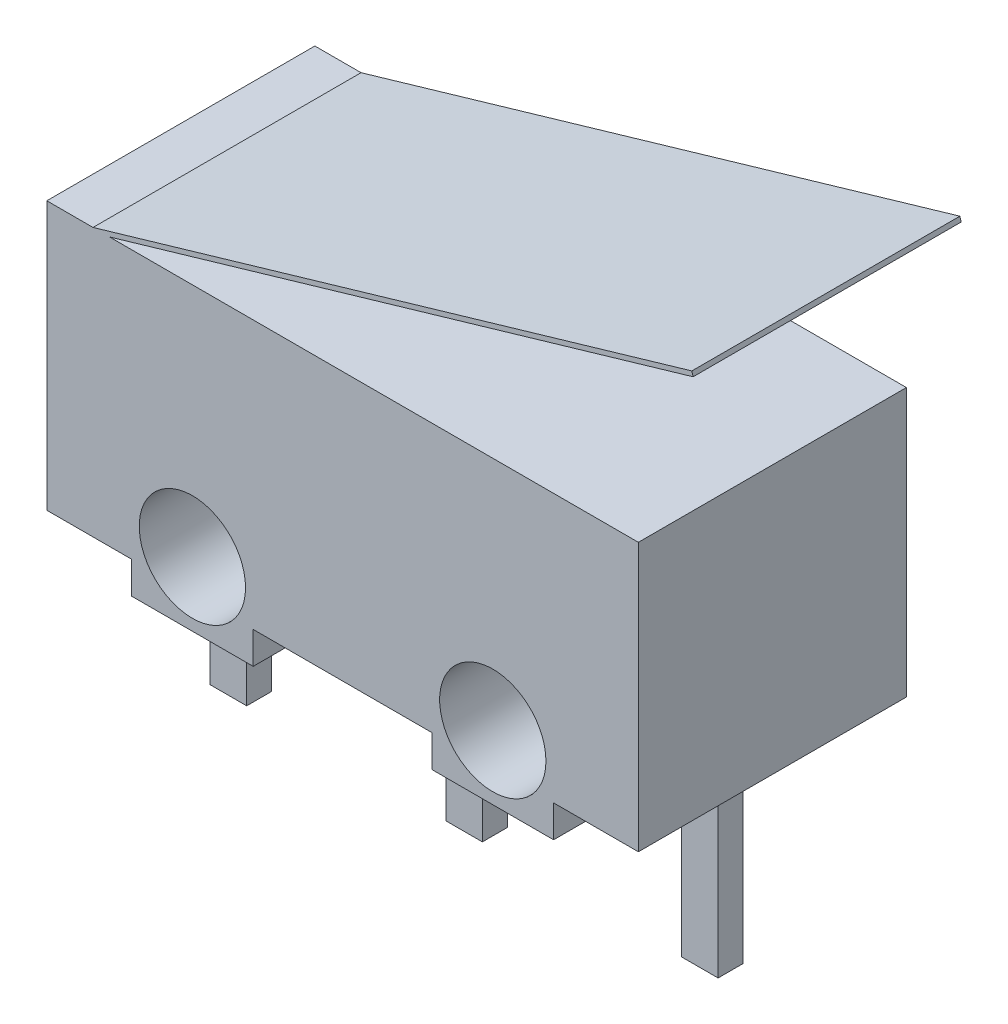
SolidWorks part; units mm, degrees
ref_plane "Front Plane" through (0, 0, 0) normal (0, 0, 1) x (1, 0, 0)
ref_plane "Top Plane" through (0, 0, 0) normal (0, 1, 0) x (1, 0, 0)
ref_plane "Right Plane" through (0, 0, 0) normal (1, 0, 0) x (0, 0, -1)
sketch "Sketch1" plane through (0, 0, 0) normal (0, 0, 1) x (1, 0, 0)
  line L0 (-6.4, -2.9) -> (-4.5658, -2.9)
  line L1 (6.4, -2.9) -> (-6.4, -2.9) construction
  line L2 (6.4, -2.9) -> (6.4, 2.9)
  line L3 (6.4, 2.9) -> (-6.4, 2.9)
  line L4 (-6.4, -2.9) -> (-6.4, 2.9)
  line L5 (6.4, -2.9) -> (-6.4, 2.9) construction
  line L6 (6.4, 2.9) -> (-6.4, -2.9) construction
  line L7 (-4.5658, -2.9) -> (-4.5658, -3.5923)
  line L8 (-4.5658, -3.5923) -> (-1.9342, -3.5923)
  line L9 (-1.9342, -3.5923) -> (-1.9342, -2.9)
  line L10 (-1.9342, -2.9) -> (1.9342, -2.9)
  line L11 (1.9342, -2.9) -> (1.9342, -3.5923)
  line L12 (1.9342, -3.5923) -> (4.5658, -3.5923)
  line L13 (4.5658, -3.5923) -> (4.5658, -2.9)
  line L14 (4.5658, -2.9) -> (6.4, -2.9)
  line L15 (0, 0) -> (0, -7.8977) construction
  circle A0 centre (-3.25, -2.2) radius 1.15
  circle A1 centre (3.25, -2.2) radius 1.15
  point P0 (0, 0)
  point P22 (-3.25, -3.5923)
  dimension "D5" = 2.3
  dimension "D1" = 5.8
  dimension "D2" = 12.8
  dimension "D3" = 6.5
  dimension "D4" = 5.1
  dimension "D6" = 0.6923
  dimension "D7" = 2.6317
extrude "Boss-Extrude1" add sketch "Sketch1" against normal mid plane 5.8
sketch "Sketch2" plane through (0, 0, 2.9) normal (0, 0, 1) x (1, 0, 0)
  line L0 (-6.4, 2.9) -> (-5.4, 2.9) construction
  line L1 (6.4, 2.9) -> (-6.4, 2.9) construction
  line L2 (-5.4, 2.9) -> (7.5571, 6.69)
  dimension "D1" = 1
  dimension "D2" = 13.5
  dimension "D3" = 9.59
extrude "Extrude-Thin1" add sketch "Sketch2" against normal up to surface (5.8 mm away) thin contours L2
ref_plane "Plane1" through (0, -7.0323, 0) normal (0, -1, 0) x (-1, 0, 0)
sketch "Sketch4" plane through (0, -7.0323, 0) normal (0, -1, 0) x (-1, 0, 0)
  line L0 (-7.6918, 0) -> (7.6918, 0) construction
  line L1 (-0.395, 0.27) -> (0.395, 0.27)
  line L2 (-0.395, 0.27) -> (-0.395, -0.27)
  line L3 (-0.395, -0.27) -> (0.395, -0.27)
  line L4 (0.395, 0.27) -> (0.395, -0.27)
  line L5 (-0.395, 0.27) -> (0.395, -0.27) construction
  line L6 (-0.395, -0.27) -> (0.395, 0.27) construction
  line L7 (5.495, 0.27) -> (4.705, 0.27)
  line L8 (5.495, 0.27) -> (5.495, -0.27)
  line L9 (5.495, -0.27) -> (4.705, -0.27)
  line L10 (4.705, 0.27) -> (4.705, -0.27)
  line L11 (5.495, 0.27) -> (4.705, -0.27) construction
  line L12 (5.495, -0.27) -> (4.705, 0.27) construction
  line L13 (0, 3.19) -> (0, -3.19) construction
  line L14 (-5.495, -0.27) -> (-4.705, 0.27) construction
  line L15 (-5.495, 0.27) -> (-4.705, -0.27) construction
  line L16 (-4.705, 0.27) -> (-4.705, -0.27)
  line L17 (-5.495, -0.27) -> (-4.705, -0.27)
  line L18 (-5.495, 0.27) -> (-5.495, -0.27)
  line L19 (-5.495, 0.27) -> (-4.705, 0.27)
  point P0 (0, 0)
  point P6 (5.1, 0)
  point P19 (-5.1, 0)
  dimension "D1" = 0.54
  dimension "D2" = 0.79
  dimension "D3" = 5.1
extrude "Boss-Extrude2" add sketch "Sketch4" against normal up to next
sketch "Sketch5" plane through (0, 2.9, 0) normal (0, 1, 0) x (1, 0, 0)
  line L0 (-7.5473, 0) -> (7.5473, 0) construction
  line L1 (-2.6, 1.425) -> (-1.71, 1.425)
  line L2 (-2.6, 1.425) -> (-2.6, -1.425)
  line L3 (-2.6, -1.425) -> (-1.71, -1.425)
  line L4 (-1.71, 1.425) -> (-1.71, -1.425)
  line L5 (-2.6, 1.425) -> (-1.71, -1.425) construction
  line L6 (-2.6, -1.425) -> (-1.71, 1.425) construction
  line L7 (-6.4, 2.9) -> (-6.4, -2.9) construction
  point P0 (-2.155, 0)
  dimension "D1" = 2.85
  dimension "D2" = 0.89
  dimension "D3" = 4.69
extrude "Boss-Extrude3" add sketch "Sketch5" along normal blind 0.56
